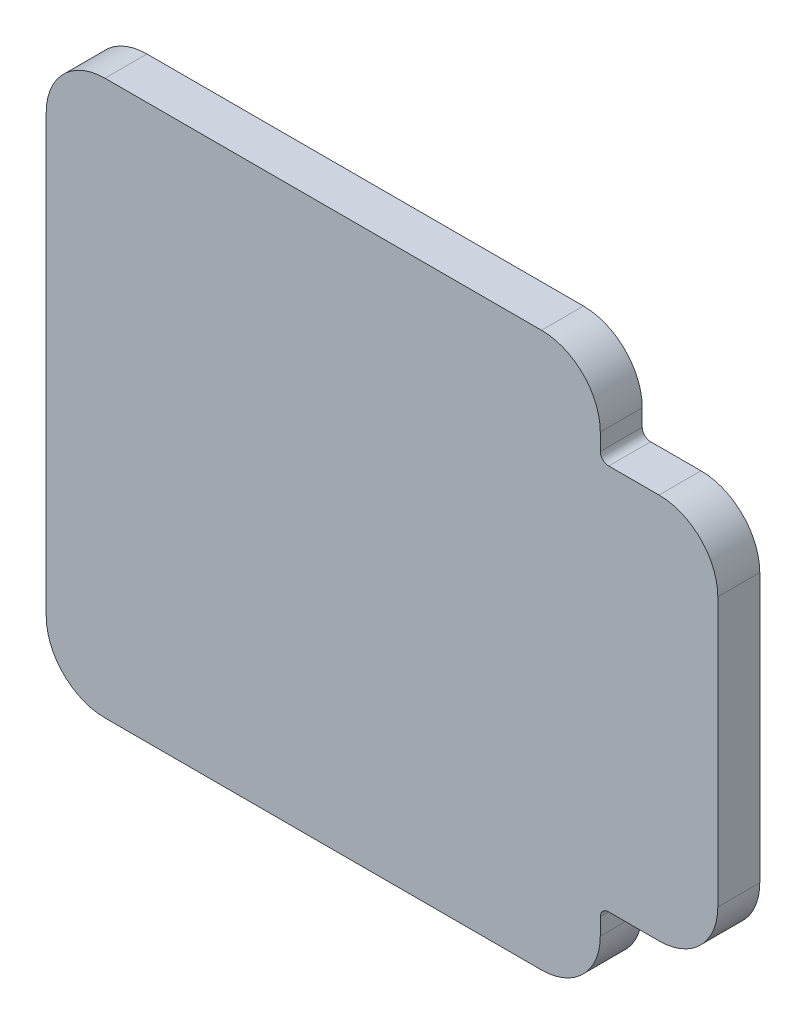
SolidWorks part; units mm, degrees
material "PVC 0.007 Plasticized"
ref_plane "Front Plane" through (0, 0, 0) normal (0, 0, 1) x (1, 0, 0)
ref_plane "Top Plane" through (0, 0, 0) normal (0, 1, 0) x (1, 0, 0)
ref_plane "Right Plane" through (0, 0, 0) normal (1, 0, 0) x (0, 0, -1)
sketch "Glass_Sketch" plane through (0, 0, 0) normal (0, 0, 1) x (1, 0, 0)
  line L0 (-6.7961, 4.8549) -> (19.2039, 4.8549)
  line L1 (21.2039, 2.8549) -> (21.2039, 1.8549)
  line L2 (23.2039, -0.1451) -> (26.2039, -0.1451)
  line L3 (28.2039, -2.1451) -> (28.2039, -18.1451)
  line L4 (26.2039, -20.1451) -> (23.2039, -20.1451)
  line L5 (21.2039, -22.1451) -> (21.2039, -23.1451)
  line L6 (19.2039, -25.1451) -> (-6.7961, -25.1451)
  line L7 (-8.7961, -23.1451) -> (-8.7961, 2.8549)
  line L8 (-10.2961, -23.1451) -> (-10.2961, 2.8549)
  line L9 (19.2039, -26.6451) -> (-6.7961, -26.6451)
  line L10 (22.7039, -22.1451) -> (22.7039, -23.1451)
  line L11 (26.2039, -21.6451) -> (23.2039, -21.6451)
  line L12 (29.7039, -2.1451) -> (29.7039, -18.1451)
  line L13 (23.2039, 1.3549) -> (26.2039, 1.3549)
  line L14 (22.7039, 2.8549) -> (22.7039, 1.8549)
  line L15 (-6.7961, 6.3549) -> (19.2039, 6.3549)
  arc A0 (-6.7961, -25.1451) -> (-8.7961, -23.1451) centre (-6.7961, -23.1451) cw
  arc A1 (21.2039, -23.1451) -> (19.2039, -25.1451) centre (19.2039, -23.1451) cw
  arc A2 (23.2039, -20.1451) -> (21.2039, -22.1451) centre (23.2039, -22.1451) ccw
  arc A3 (28.2039, -18.1451) -> (26.2039, -20.1451) centre (26.2039, -18.1451) cw
  arc A4 (26.2039, -0.1451) -> (28.2039, -2.1451) centre (26.2039, -2.1451) cw
  arc A5 (21.2039, 1.8549) -> (23.2039, -0.1451) centre (23.2039, 1.8549) ccw
  arc A6 (19.2039, 4.8549) -> (21.2039, 2.8549) centre (19.2039, 2.8549) cw
  arc A7 (-6.7961, 4.8549) -> (-8.7961, 2.8549) centre (-6.7961, 2.8549) ccw
  arc A8 (-6.7961, 6.3549) -> (-10.2961, 2.8549) centre (-6.7961, 2.8549) ccw
  arc A9 (-6.7961, -26.6451) -> (-10.2961, -23.1451) centre (-6.7961, -23.1451) cw
  arc A10 (22.7039, -23.1451) -> (19.2039, -26.6451) centre (19.2039, -23.1451) cw
  arc A11 (23.2039, -21.6451) -> (22.7039, -22.1451) centre (23.2039, -22.1451) ccw
  arc A12 (29.7039, -18.1451) -> (26.2039, -21.6451) centre (26.2039, -18.1451) cw
  arc A13 (26.2039, 1.3549) -> (29.7039, -2.1451) centre (26.2039, -2.1451) cw
  arc A14 (22.7039, 1.8549) -> (23.2039, 1.3549) centre (23.2039, 1.8549) ccw
  arc A15 (19.2039, 6.3549) -> (22.7039, 2.8549) centre (19.2039, 2.8549) cw
  point P10 (-8.7961, -25.1451)
  point P13 (21.2039, -25.1451)
  point P18 (28.2039, -20.1451)
  point P21 (28.2039, -0.1451)
  point P26 (21.2039, 4.8549)
  point P29 (-8.7961, 4.8549)
  point P30 (0, 0)
  dimension "D6" = 2
  dimension "D1" = 30
  dimension "D2" = 30
  dimension "D3" = 30
  dimension "D4" = 20
  dimension "D5" = 5
  dimension "D7" = 7
  dimension "D8" = 1.5
extrude "Boss-Extrude2" add sketch "Glass_Sketch" along normal blind 2.5 contours L8 A8 L15 A15 L14 A14 L13 A13 L12 A12 L11 A11 L10 A10 L9 A9
